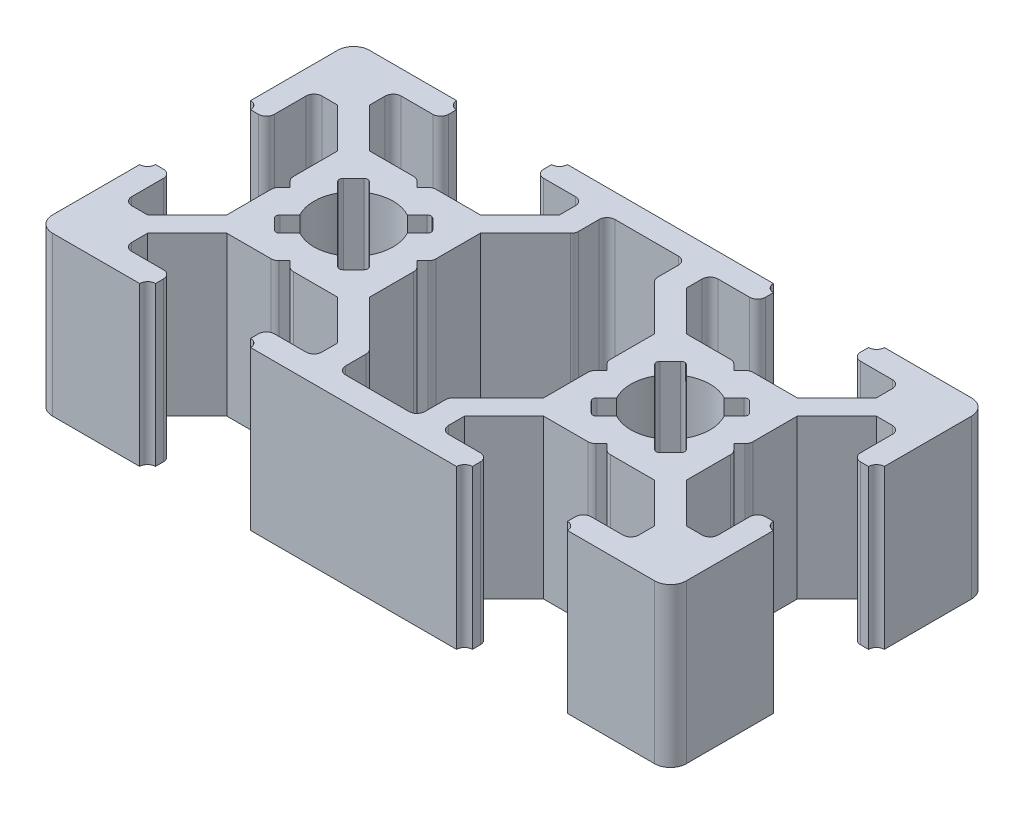
SolidWorks part; units mm, degrees
ref_plane "Front Plane" through (0, 0, 0) normal (0, 0, 1) x (1, 0, 0)
ref_plane "Top Plane" through (0, 0, 0) normal (0, 1, 0) x (1, 0, 0)
ref_plane "Right Plane" through (0, 0, 0) normal (1, 0, 0) x (0, 0, -1)
sketch "Sketch2" plane through (0, 0, 0) normal (0, 1, 0) x (1, 0, 0)
  line L0 (0, 13) -> (1.5, 13)
  line L1 (0, 0) -> (40, 0)
  line L2 (0, 0) -> (0, 20)
  line L3 (0, 20) -> (40, 20)
  line L4 (40, 0) -> (40, 20)
  line L9 (5.5, 6.5) -> (3, 4)
  line L10 (3, 4) -> (1.5, 4)
  line L11 (1.5, 4) -> (1.5, 7)
  line L12 (1.5, 7) -> (0, 7)
  line L13 (0, 7) -> (0, 13)
  line L14 (1.5, 13) -> (1.5, 16)
  line L15 (1.5, 16) -> (3, 16)
  line L16 (3, 16) -> (5.5, 13.5)
  line L17 (5.5, 10.5) -> (6, 10)
  line L18 (6, 10) -> (5.5, 9.5)
  line L19 (5.5, 9.5) -> (5.5, 10.5)
  line L20 (20, 20) -> (20, 0) construction
  line L31 (7, 18.5) -> (7, 20)
  line L32 (7, 18.5) -> (4, 18.5)
  line L33 (4, 18.5) -> (4, 17)
  line L34 (4, 17) -> (6.5, 14.5)
  line L38 (16, 18.5) -> (13, 18.5)
  line L39 (13, 18.5) -> (13, 20)
  line L40 (7, 20) -> (13, 20)
  line L41 (16, 18.5) -> (16, 17)
  line L42 (16, 17) -> (13.5, 14.5)
  line L53 (0, 10) -> (40, 10) construction
  line L89 (17.5, 18.5) -> (22.5, 18.5)
  line L90 (22.5, 18.5) -> (22.5, 16.5)
  line L91 (22.5, 16.5) -> (25.5, 13.5)
  line L92 (25.5, 13.5) -> (25.5, 6.5)
  line L93 (25.5, 6.5) -> (22.5, 3.5)
  line L94 (22.5, 3.5) -> (22.5, 1.5)
  line L95 (22.5, 1.5) -> (17.5, 1.5)
  line L96 (17.5, 1.5) -> (17.5, 3.5)
  line L97 (17.5, 3.5) -> (14.5, 6.5)
  line L98 (14.5, 6.5) -> (14.5, 13.5)
  line L99 (14.5, 13.5) -> (17.5, 16.5)
  line L100 (17.5, 16.5) -> (17.5, 18.5)
  line L102 (5.5, 13.5) -> (5.5, 10)
  line L103 (5.5, 10) -> (5.5, 6.5)
  line L104 (13.5, 14.5) -> (10, 14.5)
  line L105 (10, 14.5) -> (6.5, 14.5)
  line L106 (14.5, 10.5) -> (14.5, 9.5)
  line L107 (14.5, 9.5) -> (14, 10)
  line L108 (14, 10) -> (14.5, 10.5)
  line L109 (7, 18.5) -> (13, 18.5) construction
  line L110 (9.5, 14.5) -> (10.5, 14.5)
  line L111 (10.5, 14.5) -> (10, 14)
  line L112 (10, 14) -> (9.5, 14.5)
  line L113 (10.5, 5.5) -> (10, 6)
  line L114 (9.5, 5.5) -> (10.5, 5.5)
  line L115 (10, 6) -> (9.5, 5.5)
  line L116 (13.5, 5.5) -> (10, 5.5)
  line L117 (16, 3) -> (13.5, 5.5)
  line L118 (16, 1.5) -> (16, 3)
  line L119 (16, 1.5) -> (13, 1.5)
  line L120 (13, 1.5) -> (13, 0)
  line L121 (7, 0) -> (13, 0)
  line L122 (7, 1.5) -> (7, 0)
  line L123 (7, 1.5) -> (4, 1.5)
  line L124 (4, 1.5) -> (4, 3)
  line L125 (4, 3) -> (6.5, 5.5)
  line L126 (10, 5.5) -> (6.5, 5.5)
  line L127 (30.5, 5.5) -> (29.5, 5.5)
  line L128 (30, 6) -> (30.5, 5.5)
  line L129 (29.5, 5.5) -> (30, 6)
  line L130 (24, 3) -> (26.5, 5.5)
  line L131 (24, 1.5) -> (24, 3)
  line L132 (24, 1.5) -> (27, 1.5)
  line L133 (27, 1.5) -> (27, 0)
  line L134 (33, 0) -> (27, 0)
  line L135 (33, 1.5) -> (33, 0)
  line L136 (33, 1.5) -> (36, 1.5)
  line L137 (36, 1.5) -> (36, 3)
  line L138 (36, 3) -> (33.5, 5.5)
  line L139 (30, 5.5) -> (33.5, 5.5)
  line L140 (26.5, 5.5) -> (30, 5.5)
  line L141 (34, 10) -> (34.5, 9.5)
  line L142 (34.5, 10.5) -> (34, 10)
  line L143 (34.5, 9.5) -> (34.5, 10.5)
  line L144 (34.5, 13.5) -> (34.5, 10)
  line L145 (37, 16) -> (34.5, 13.5)
  line L146 (38.5, 16) -> (37, 16)
  line L147 (38.5, 13) -> (38.5, 16)
  line L148 (40, 13) -> (38.5, 13)
  line L149 (40, 7) -> (40, 13)
  line L150 (38.5, 7) -> (40, 7)
  line L151 (38.5, 4) -> (38.5, 7)
  line L152 (37, 4) -> (38.5, 4)
  line L153 (34.5, 6.5) -> (37, 4)
  line L154 (34.5, 10) -> (34.5, 6.5)
  line L155 (29.5, 14.5) -> (30, 14)
  line L156 (30.5, 14.5) -> (29.5, 14.5)
  line L157 (30, 14) -> (30.5, 14.5)
  line L158 (26.5, 14.5) -> (30, 14.5)
  line L159 (24, 17) -> (26.5, 14.5)
  line L160 (24, 18.5) -> (24, 17)
  line L161 (24, 18.5) -> (27, 18.5)
  line L162 (27, 18.5) -> (27, 20)
  line L163 (33, 20) -> (27, 20)
  line L164 (33, 18.5) -> (33, 20)
  line L165 (33, 18.5) -> (36, 18.5)
  line L166 (36, 18.5) -> (36, 17)
  line L167 (36, 17) -> (33.5, 14.5)
  line L168 (30, 14.5) -> (33.5, 14.5)
  line L169 (13.5, 14.5) -> (14.5, 13.5) construction
  line L170 (5.5, 6.5) -> (6.5, 5.5) construction
  line L171 (6.5, 14.5) -> (5.5, 13.5) construction
  line L172 (14.5, 6.5) -> (13.5, 5.5) construction
  line L173 (14.5, 10.5) -> (10.5, 14.5) construction
  line L174 (10.5, 5.5) -> (14.5, 9.5) construction
  line L175 (9.5, 5.5) -> (5.5, 9.5) construction
  line L176 (5.5, 10.5) -> (9.5, 14.5) construction
  line L177 (12, 13) -> (13, 12)
  line L178 (13, 12) -> (8, 7)
  line L179 (8, 7) -> (7, 8)
  line L180 (7, 8) -> (12, 13)
  line L181 (8, 13) -> (13, 8)
  line L182 (13, 8) -> (12, 7)
  line L183 (12, 7) -> (7, 12)
  line L184 (7, 12) -> (8, 13)
  line L185 (28, 7) -> (33, 12)
  line L186 (27, 8) -> (28, 7)
  line L187 (32, 13) -> (27, 8)
  line L188 (33, 12) -> (32, 13)
  line L189 (32, 7) -> (33, 8)
  line L190 (27, 12) -> (32, 7)
  line L191 (28, 13) -> (27, 12)
  line L192 (33, 8) -> (28, 13)
  line L193 (13.5, 20) -> (13, 20)
  line L194 (13, 19.5) -> (13, 20)
  line L195 (6.5, 20) -> (7, 20)
  line L196 (0, 13.5) -> (0, 13)
  line L197 (0.25, 7) -> (0, 7)
  line L198 (7, 19.5) -> (7, 20)
  line L199 (0.25, 7) -> (0, 7)
  line L200 (33, 19.5) -> (33, 20)
  line L201 (33.5, 20) -> (33, 20)
  line L202 (27, 19.5) -> (27, 20)
  line L203 (26.5, 20) -> (27, 20)
  line L204 (33, 0.5) -> (33, 0)
  line L205 (33.5, 0) -> (33, 0)
  line L206 (27, 0.5) -> (27, 0)
  line L207 (26.5, 0) -> (27, 0)
  line L208 (13, 0.5) -> (13, 0)
  line L209 (13.5, 0) -> (13, 0)
  line L210 (7, 0.5) -> (7, 0)
  line L211 (6.5, 0) -> (7, 0)
  line L212 (0.5, 13) -> (0, 13)
  line L213 (0, 6.75) -> (0, 7)
  line L214 (0, 6.75) -> (0, 7)
  line L215 (0, 7) -> (0.25, 7)
  line L216 (0, 6.5) -> (0, 7)
  line L217 (0, 7) -> (0.5, 7)
  line L218 (39.5, 13) -> (40, 13)
  line L219 (40, 13.5) -> (40, 13)
  line L220 (40, 6.5) -> (40, 7)
  line L221 (40, 7) -> (39.5, 7)
  line L222 (25.5, 9.5) -> (26, 10)
  line L223 (25.5, 10.5) -> (25.5, 9.5)
  line L224 (26, 10) -> (25.5, 10.5)
  circle A0 centre (10, 10) radius 2.5
  circle A1 centre (30, 10) radius 2.5
  arc A2 (13.5, 20) -> (13, 19.5) centre (13, 20) cw
  arc A3 (7, 19.5) -> (6.5, 20) centre (7, 20) cw
  arc A4 (0.5, 13) -> (0, 13.5) centre (0, 13) ccw
  arc A5 (0.5, 7) -> (0, 6.5) centre (0, 7) cw
  arc A6 (33, 19.5) -> (33.5, 20) centre (33, 20) ccw
  arc A7 (26.5, 20) -> (27, 19.5) centre (27, 20) ccw
  arc A8 (33, 0.5) -> (33.5, 0) centre (33, 0) cw
  arc A9 (26.5, 0) -> (27, 0.5) centre (27, 0) cw
  arc A10 (13.5, 0) -> (13, 0.5) centre (13, 0) ccw
  arc A11 (7, 0.5) -> (6.5, 0) centre (7, 0) ccw
  arc A12 (39.5, 13) -> (40, 13.5) centre (40, 13) cw
  arc A13 (39.5, 7) -> (40, 6.5) centre (40, 7) ccw
  point P19 (20, 10)
  point P103 (14.5, 10)
  dimension "D31" = 5
  dimension "D32" = 0.5
  dimension "D33" = 0.5
  dimension "D34" = 0.5
  dimension "D35" = 0.5
  dimension "D1" = 40
  dimension "D2" = 20
  dimension "D3" = 7
  dimension "D4" = 7
  dimension "D5" = 1.5
  dimension "D6" = 1.5
  dimension "D7" = 3.5
  dimension "D8" = 1.5
  dimension "D9" = 1.5
  dimension "D10" = 3
  dimension "D11" = 3
  dimension "D12" = 3.5
  dimension "D13" = 0.5
  dimension "D14" = 0.5
  dimension "D15" = 7
  dimension "D16" = 6
  dimension "D17" = 1.5
  dimension "D18" = 1.5
  dimension "D19" = 3
  dimension "D20" = 3
  dimension "D21" = 0.5
  dimension "D22" = 1.5
  dimension "D23" = 5.5
  dimension "D24" = 0.5
  dimension "D25" = 0.5
  dimension "D26" = 1.5
  dimension "D27" = 1.5
  dimension "D28" = 2
  dimension "D29" = 2
  dimension "D30" = 0.5
extrude "Boss-Extrude1" add sketch "Sketch2" along normal blind 10 contours L168 L157 L155 L158 L159 L160 L161 L162 L3 L39 L38 L41 L42 L104 L111 L112 L105 L34 L33 L32 L31 L2 L0 L14 L15 L16 L102 L17 L18 L103 L9 L10 L11 L12 L1 L122 L123 L124 L125 L126 L115 L113 L116 L117 L118 L119 L120 L133
fillet "Fillet1" radius 1 4 edges at (40, 5, -20) (40, 5, 0) (0, 5, 0) (0, 5, -20)
fillet "Fillet2" radius 0.5 6 edges at (13, 5, -18.5) (16, 5, -18.5) (10.5, 5, -14.5) (9.5, 5, -14.5) (4, 5, -18.5) (7, 5, -18.5)
fillet "Fillet3" radius 0.25 8 edges at (8, 5, -7) (7, 5, -8) (12, 5, -7) (13, 5, -8) (13, 5, -12) (12, 5, -13) (7, 5, -12) (8, 5, -13)
fillet "Fillet5" radius 0.25 8 edges at (27, 5, -8) (28, 5, -7) (32, 5, -7) (33, 5, -8) (33, 5, -12) (32, 5, -13) (27, 5, -12) (28, 5, -13)
fillet "Fillet6" radius 0.5 30 edges at (36, 5, -18.5) (33, 5, -18.5) (30.5, 5, -14.5) (29.5, 5, -14.5) (24, 5, -18.5) (27, 5, -18.5) (38.5, 5, -4) (38.5, 5, -7) (34.5, 5, -9.5) (34.5, 5, -10.5) (38.5, 5, -16) (38.5, 5, -13) (24, 5, -1.5) (27, 5, -1.5) (29.5, 5, -5.5) (30.5, 5, -5.5) (36, 5, -1.5) (33, 5, -1.5) (4, 5, -1.5) (7, 5, -1.5) (9.5, 5, -5.5) (10.5, 5, -5.5) (16, 5, -1.5) (13, 5, -1.5) (5.5, 5, -10.5) (5.5, 5, -9.5) (1.5, 5, -4) (1.5, 5, -7) (1.5, 5, -16) (1.5, 5, -13)
fillet "Fillet7" radius 0.5 8 edges at (22.5, 5, -3.5) (22.5, 5, -1.5) (17.5, 5, -3.5) (17.5, 5, -1.5) (17.5, 5, -16.5) (22.5, 5, -16.5) (22.5, 5, -18.5) (17.5, 5, -18.5)
fillet "Fillet8" radius 0.5 4 edges at (25.5, 5, -9.5) (25.5, 5, -10.5) (14.5, 5, -9.5) (14.5, 5, -10.5)
